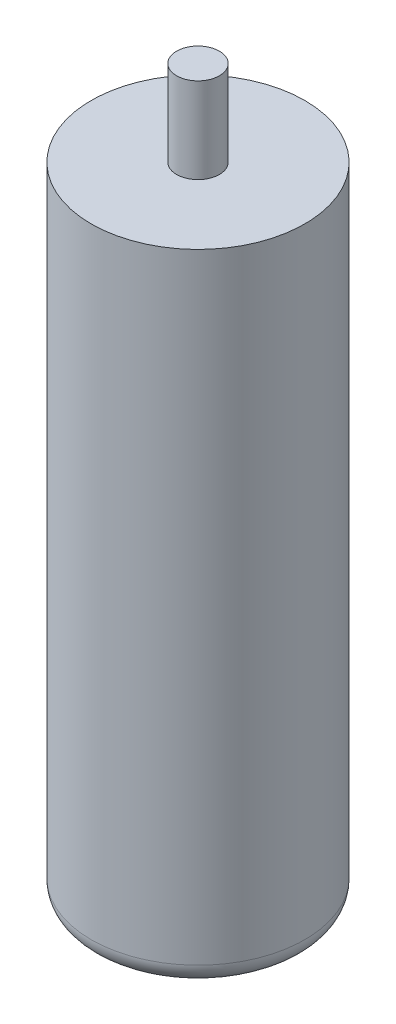
SolidWorks part; units mm, degrees
ref_plane "Front Plane" through (0, 0, 0) normal (0, 0, 1) x (1, 0, 0)
ref_plane "Top Plane" through (0, 0, 0) normal (0, 1, 0) x (1, 0, 0)
ref_plane "Right Plane" through (0, 0, 0) normal (1, 0, 0) x (0, 0, -1)
sketch "Sketch1" plane through (0, 0, 0) normal (0, 1, 0) x (1, 0, 0)
  circle A0 centre (0, 0) radius 25
  dimension "D1" = 50
extrude "Boss-Extrude1" add sketch "Sketch1" along normal blind 150
sketch "Sketch2" plane through (0, 150, 0) normal (0, 1, 0) x (1, 0, 0)
  circle A0 centre (0, 0) radius 5
  dimension "D1" = 10
extrude "Boss-Extrude2" add sketch "Sketch2" along normal blind 20
fillet "Fillet1" radius 5 1 edges at (0, 0, 25)
